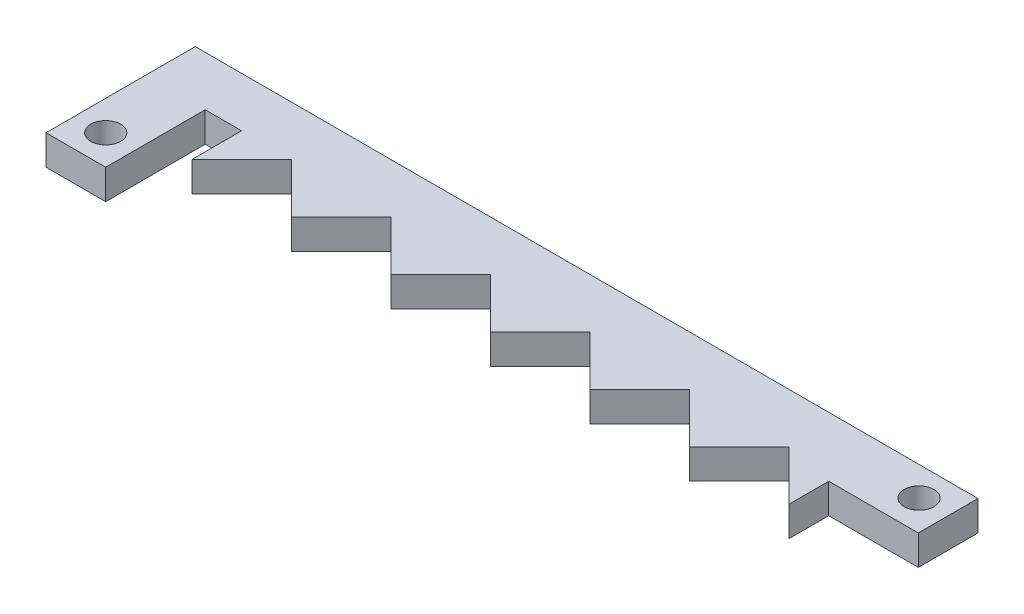
SolidWorks part; units mm, degrees
material "Custom Plastic"
ref_plane "Front Plane" through (0, 0, 0) normal (0, 0, 1) x (1, 0, 0)
ref_plane "Top Plane" through (0, 0, 0) normal (0, 1, 0) x (1, 0, 0)
ref_plane "Right Plane" through (0, 0, 0) normal (1, 0, 0) x (0, 0, -1)
sketch "Sketch1" plane through (0, 0, 0) normal (0, 1, 0) x (1, 0, 0)
  line L1 (1.7658, 34.484) -> (6.7658, 39.484)
  line L2 (6.7658, 39.484) -> (11.7658, 34.484)
  line L3 (11.7658, 34.484) -> (16.7658, 39.484)
  line L4 (16.7658, 39.484) -> (21.7658, 34.484)
  line L5 (21.7658, 34.484) -> (26.7658, 39.484)
  line L6 (26.7658, 39.484) -> (31.7658, 34.484)
  line L15 (1, 44.484) -> (70.7658, 44.484)
  line L26 (-5.8488, 44.484) -> (-7.8912, 44.484)
  line L27 (1, 44.484) -> (-5.8488, 44.484)
  line L28 (-7.8912, 44.484) -> (-7.8912, 29.484)
  line L29 (-7.8912, 29.484) -> (-1.8912, 29.484)
  line L30 (-1.8912, 29.484) -> (-1.8912, 39.484)
  line L31 (-1.8912, 39.484) -> (1.7658, 39.484)
  line L32 (-7.8912, 32.484) -> (-1.8912, 32.484) construction
  line L34 (70.7658, 44.484) -> (70.7658, 38.484)
  line L35 (70.7658, 38.484) -> (61.7658, 38.484)
  line L36 (67.7658, 44.6315) -> (67.7658, 38.484) construction
  line L37 (31.7658, 34.484) -> (36.7658, 39.484)
  line L38 (36.7658, 39.484) -> (41.7658, 34.484)
  line L39 (41.7658, 34.484) -> (46.7658, 39.484)
  line L40 (46.7658, 39.484) -> (51.7658, 34.484)
  line L41 (1.7658, 39.484) -> (1.7658, 34.484)
  line L44 (61.7658, 38.484) -> (61.7658, 34.484)
  line L45 (51.7658, 34.484) -> (56.7658, 39.484)
  line L46 (56.7658, 39.484) -> (61.7658, 34.484)
  circle A2 centre (-4.8912, 32.484) radius 1.5
  circle A3 centre (67.7658, 41.5578) radius 1.5
  point P2 (0, 0)
  point P20 (0, 0)
  point P23 (0, 0)
  point P24 (0, 0)
  dimension "D7" = 3
  dimension "D9" = 60
  dimension "D11" = 3
  dimension "D2" = 5
  dimension "D3" = 6
  dimension "D5" = 15
  dimension "D8" = 3
  dimension "D10" = 6
  dimension "D12" = 3
  dimension "D14" = 10
  dimension "D15" = 5
  dimension "D16" = 9
  dimension "D4" = 6
extrude "Boss-Extrude1" add sketch "Sketch1" along normal blind 3
